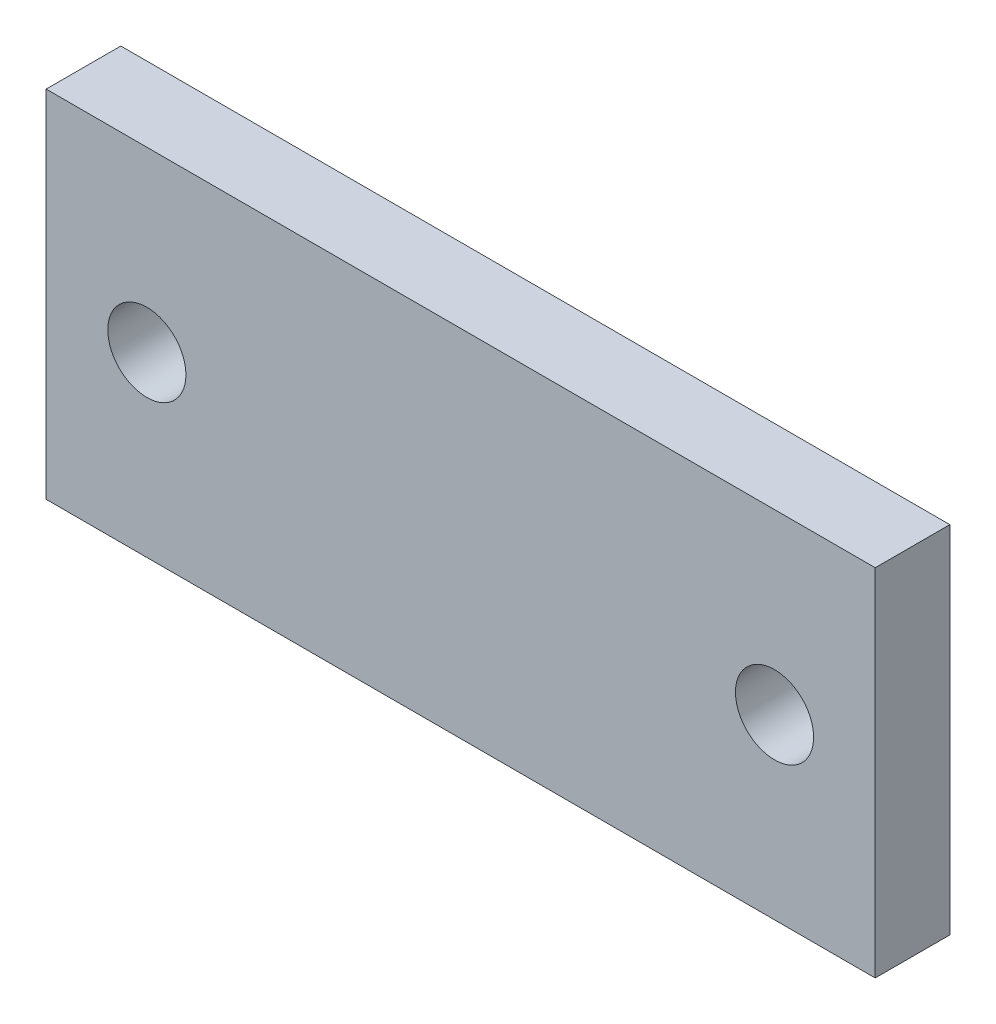
SolidWorks part; units mm, degrees
ref_plane "前视基准面" through (0, 0, 0) normal (0, 0, 1) x (1, 0, 0)
ref_plane "上视基准面" through (0, 0, 0) normal (0, 1, 0) x (1, 0, 0)
ref_plane "右视基准面" through (0, 0, 0) normal (1, 0, 0) x (0, 0, -1)
sketch "草图1" plane through (0, 0, 0) normal (0, 0, 1) x (1, 0, 0)
  line L0 (0, -15) -> (0, 15) construction
  line L1 (35, -15) -> (-35, -15)
  line L2 (35, -15) -> (35, 15)
  line L3 (35, 15) -> (-35, 15)
  line L4 (-35, -15) -> (-35, 15)
  line L5 (35, -15) -> (-35, 15) construction
  line L6 (35, 15) -> (-35, -15) construction
  line L7 (0, 0) -> (-35, 0) construction
  circle A0 centre (-26.5, 0) radius 3.3
  circle A1 centre (26.5, 0) radius 3.3
  point P0 (0, 0)
  dimension "D4" = 6.6
  dimension "D1" = 70
  dimension "D2" = 30
  dimension "D3" = 53
extrude "凸台-拉伸1" add sketch "草图1" along normal blind 6.3
